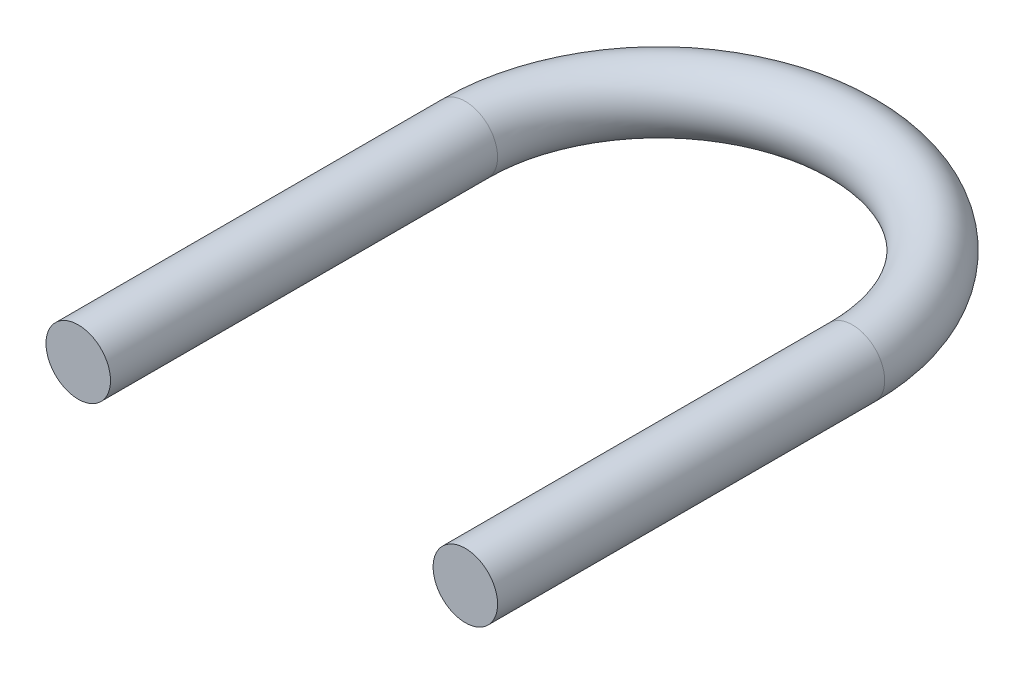
SolidWorks part; units mm, degrees
ref_plane "Front Plane" through (0, 0, 0) normal (0, 0, 1) x (1, 0, 0)
ref_plane "Top Plane" through (0, 0, 0) normal (0, 1, 0) x (1, 0, 0)
ref_plane "Right Plane" through (0, 0, 0) normal (1, 0, 0) x (0, 0, -1)
sketch "Sketch2" plane through (0, 0, 0) normal (0, 1, 0) x (1, 0, 0)
  line L1 (0, 0) -> (355.6, 0)
  line L2 (0, 0) -> (0, 292.1)
  line L3 (0, 292.1) -> (355.6, 292.1)
  line L4 (355.6, 0) -> (355.6, 292.1)
  line L6 (-153.5056, 292.1) -> (0, 292.1)
  dimension "D1" = 292.1
  dimension "D2" = 355.6
ref_plane "Plane1" through (0, 1676.4, 0) normal (0, 1, 0) x (1, 0, 0)
sketch "Sketch3" plane through (0, 1676.4, 0) normal (0, 1, 0) x (1, 0, 0)
  line L0 (25.4, 419.1) -> (25.4, 723.9)
  line L2 (0, 0) -> (355.6, 0) construction
  line L4 (177.8, 0) -> (177.8, 419.1) construction
  line L5 (-50.8, 0) -> (406.4, 0)
  line L6 (-127, 419.1) -> (482.6, 419.1)
  line L7 (-127, 419.1) -> (-50.8, 0)
  line L8 (482.6, 419.1) -> (406.4, 0)
  line L9 (330.2, 419.1) -> (330.2, 723.9)
  arc A0 (25.4, 723.9) -> (330.2, 723.9) centre (177.8, 723.9) cw
  point P4 (177.8, 0)
  point P7 (177.8, 0)
  point P11 (177.8, 419.1)
  point P17 (177.8, 876.3)
  dimension "D6" = 304.8
  dimension "D1" = 457.2
  dimension "D2" = 419.1
  dimension "D3" = 609.6
  dimension "D4" = 152.4
  dimension "D5" = 152.4
sketch3d "3DSketch5"
  line L0 (0, 0, -292.1) -> (0, 457.2, -292.1)
  line L1 (0, 0, 0) -> (0, 457.2, 0)
  line L2 (355.6, 0, -292.1) -> (355.6, 457.2, -292.1)
  line L3 (355.6, 0, 0) -> (355.6, 457.2, 0)
  line L4 (355.6, 457.2, -292.1) -> (355.6, 457.2, 0)
  line L5 (355.6, 457.2, -292.1) -> (482.6, 1676.4, -419.1)
  line L6 (0, 457.2, -292.1) -> (-127, 1676.4, -419.1)
  line L7 (355.6, 457.2, 0) -> (406.4, 1676.4, 0)
  line L8 (0, 457.2, 0) -> (-50.8, 1676.4, 0)
  line L9 (0, 457.2, -292.1) -> (0, 457.2, 0)
  line L10 (355.6, 457.2, 0) -> (355.6, 0, -292.1)
  line L11 (0, 457.2, 0) -> (0, 0, -292.1)
  line L12 (-71.5818, 1676.4, -114.3) -> (427.1818, 1676.4, -114.3)
  line L13 (355.6, 457.2, 0) -> (401.4077, 896.954, -337.9077)
  line L14 (401.4077, 896.954, -337.9077) -> (387.8952, 1232.2853, 0)
  line L15 (387.8952, 1232.2853, 0) -> (482.6, 1676.4, -419.1)
  line L16 (0, 457.2, 0) -> (-45.8077, 896.954, -337.9077)
  line L17 (-45.8077, 896.954, -337.9077) -> (-32.2952, 1232.2853, 0)
  line L18 (-32.2952, 1232.2853, 0) -> (-127, 1676.4, -419.1)
  line L19 (355.6, 0, 0) -> (0, 0, -292.1)
  line L20 (355.6, 457.2, -292.1) -> (0, 457.2, -292.1)
  line L21 (-31.411, 758.7456, -323.511) -> (387.011, 758.7456, -323.511) construction
  line L22 (387.011, 758.7456, -323.511) -> (387.011, 746.9034, -437.1959)
  line L23 (-19.6319, 645.666, -311.7319) -> (-31.411, 746.9034, -437.1959)
  line L24 (387.011, 746.9034, -437.1959) -> (375.2319, 645.666, -311.7319)
  line L25 (387.011, 746.9034, -437.1959) -> (-31.411, 746.9034, -437.1959)
  line L27 (-127, 1676.4, -419.1) -> (-50.8, 1676.4, 0) construction
  line L28 (482.6, 1676.4, -419.1) -> (406.4, 1676.4, 0) construction
  line L29 (-50.8, 1676.4, 0) -> (406.4, 1676.4, 0) construction
  line L30 (0, 457.2, 0) -> (355.6, 457.2, 0)
  line L31 (-32.2952, 1232.2853, 0) -> (387.8952, 1232.2853, 0)
  line L32 (-15.3619, 825.8853, 0) -> (370.9619, 825.8853, 0)
  line L33 (-31.411, 746.9034, -437.1959) -> (-31.411, 758.7456, -323.511)
  point P27 (-45.8038, 896.9163, -337.9038)
  dimension "D1" = 457.2
  dimension "D2" = 457.2
  dimension "D3" = 457.2
  dimension "D4" = 457.2
  dimension "D5" = 444.5
  dimension "D6" = 444.5
  dimension "D7" = 444.5
  dimension "D8" = 114.3
  dimension "16.2" = 444.5
  dimension "D9" = 45
  dimension "D10" = 304.8
  dimension "D12" = 114.3
  dimension "D11" = 304.8
  dimension "D13" = 45
  dimension "D14" = 114.3
  dimension "D15" = 406.4
ref_plane "Plane2" through (0, 896.954, 0) normal (0, 1, 0) x (1, 0, 0)
ref_plane "Plane3" through (0, 0, -419.1) normal (0, 0, 1) x (1, 0, 0)
sketch "Sketch4" plane through (0, 0, -419.1) normal (0, 0, 1) x (1, 0, 0)
  circle A0 centre (330.2, 1676.4) radius 25.4
  dimension "D1" = 50.8
sweep "Sweep1" add profiles "Sketch4" path "Sketch3"
sketch "Sketch5" plane through (0, 0, -723.9) normal (0, 0, -1) x (-1, 0, 0)
sketch "Sketch6" plane through (0, 0, -723.9) normal (0, 0, -1) x (-1, 0, 0)
  circle A1 centre (-330.2, 1676.4) radius 25.4
  circle A2 centre (-330.2, 1676.4) radius 25.4
  dimension "D1" = 0
sketch "Sketch7" plane through (0, 0, -419.1) normal (0, 0, 1) x (1, 0, 0)
  circle A0 centre (25.4, 1676.4) radius 25.4
  dimension "D1" = 50.8
sketch3d "3DSketch6"
  line L0 (25.4, 1676.4, -419.1) -> (25.4, 1676.4, -723.9) construction
  line L1 (25.4, 1676.4, -419.1) -> (25.4, 1676.4, -723.9)
  arc A0 (25.4, 1676.4, -723.9) -> (330.2, 1676.4, -723.9) centre (177.8, 1676.4, -723.9) ccw construction
  arc A1 (25.4, 1676.4, -723.9) -> (330.2, 1676.4, -723.9) centre (177.8, 1676.4, -723.9) ccw
  point P5 (177.8, 1524, -723.9)
  point P6 (177.8, 1524, -723.9)
sweep "Sweep2" add profiles "Sketch7" path "3DSketch6"
